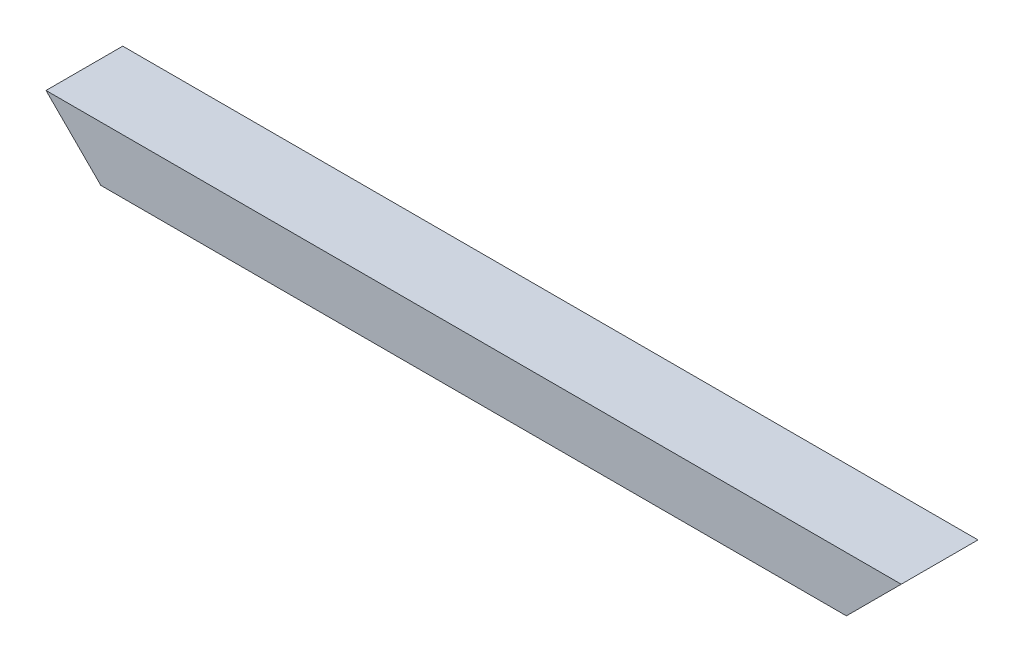
SolidWorks part; units mm, degrees
material "1023 Carbon Steel Sheet (SS)"
ref_plane "Front Plane" through (0, 0, 0) normal (0, 0, 1) x (1, 0, 0)
ref_plane "Top Plane" through (0, 0, 0) normal (0, 1, 0) x (1, 0, 0)
ref_plane "Right Plane" through (0, 0, 0) normal (1, 0, 0) x (0, 0, -1)
sketch "Sketch2" plane through (0, 0, 0) normal (0, 0, 1) x (1, 0, 0)
  line L0 (0, 0) -> (863.6, 0)
  line L1 (863.6, 0) -> (927.1, 63.5)
  line L2 (927.1, 63.5) -> (-63.5, 63.5)
  line L3 (-63.5, 63.5) -> (0, 0)
  dimension "D1" = 135
  dimension "D2" = 135
  dimension "D3" = 863.6
  dimension "D4" = 63.5
extrude "Boss-Extrude1" add sketch "Sketch2" along normal blind 88.9
